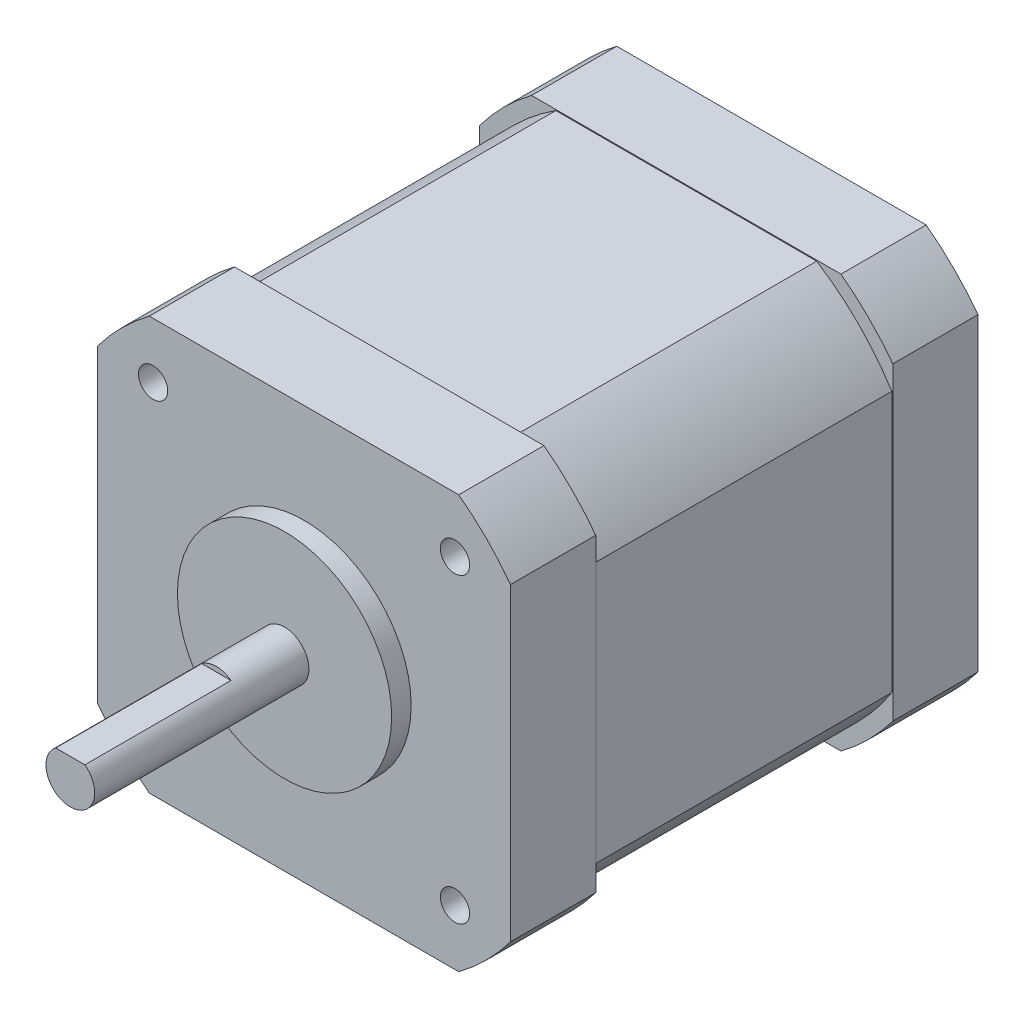
SolidWorks part; units mm, degrees
ref_plane "Front Plane" through (0, 0, 0) normal (0, 0, 1) x (1, 0, 0)
ref_plane "Top Plane" through (0, 0, 0) normal (0, 1, 0) x (1, 0, 0)
ref_plane "Right Plane" through (0, 0, 0) normal (1, 0, 0) x (0, 0, -1)
sketch "Sketch1" plane through (0, 0, 0) normal (0, 0, 1) x (1, 0, 0)
  line L0 (-21.209, 15.888) -> (-21.209, -15.888)
  line L1 (-15.888, -21.209) -> (15.888, -21.209)
  line L2 (21.209, -15.888) -> (21.209, 15.888)
  line L3 (15.888, 21.209) -> (-15.888, 21.209)
  arc A0 (-15.888, 21.209) -> (-21.209, 15.888) centre (0, 0) ccw
  arc A1 (-21.209, -15.888) -> (-15.888, -21.209) centre (0, 0) ccw
  arc A2 (15.888, -21.209) -> (21.209, -15.888) centre (0, 0) ccw
  arc A3 (21.209, 15.888) -> (15.888, 21.209) centre (0, 0) ccw
extrude "Boss-Extrude1" add sketch "Sketch1" against normal blind 8.75
sketch "Sketch2" plane through (0, 0, -8.75) normal (0, 0, -1) x (-1, 0, 0)
  line L0 (-13.3944, 21.109) -> (13.3944, 21.109)
  line L1 (21.109, 13.3944) -> (21.109, -13.3944)
  line L2 (13.3944, -21.109) -> (-13.3944, -21.109)
  line L3 (-21.109, -13.3944) -> (-21.109, 13.3944)
  arc A0 (-21.109, 13.3944) -> (-13.3944, 21.109) centre (0, 0) cw
  arc A1 (13.3944, 21.109) -> (21.109, 13.3944) centre (0, 0) cw
  arc A2 (21.109, -13.3944) -> (13.3944, -21.109) centre (0, 0) cw
  arc A3 (-13.3944, -21.109) -> (-21.109, -13.3944) centre (0, 0) cw
extrude "Boss-Extrude2" add sketch "Sketch2" along normal blind 30.5
ref_plane "Plane1" through (0, 0, -39.25) normal (0, 0, 1) x (1, 0, 0)
sketch "Sketch3" plane through (0, 0, -39.25) normal (0, 0, 1) x (1, 0, 0)
  line L0 (-15.888, -21.209) -> (15.888, -21.209)
  line L1 (21.209, -15.888) -> (21.209, 15.888)
  line L2 (15.888, 21.209) -> (-15.888, 21.209)
  line L3 (-21.209, 15.888) -> (-21.209, -15.888)
  arc A0 (-21.209, -15.888) -> (-15.888, -21.209) centre (0, 0) ccw
  arc A1 (15.888, -21.209) -> (21.209, -15.888) centre (0, 0) ccw
  arc A2 (21.209, 15.888) -> (15.888, 21.209) centre (0, 0) ccw
  arc A3 (-15.888, 21.209) -> (-21.209, 15.888) centre (0, 0) ccw
extrude "Boss-Extrude3" add sketch "Sketch3" against normal blind 8.75
sketch "Sketch4" plane through (0, 0, 0) normal (0, 0, 1) x (1, 0, 0)
  circle A0 centre (0, 0) radius 11
extrude "Boss-Extrude4" add sketch "Sketch4" along normal blind 2
sketch "Sketch5" plane through (0, 0, 2) normal (0, 0, 1) x (1, 0, 0)
  circle A0 centre (0, 0) radius 2.5
extrude "Boss-Extrude5" add sketch "Sketch5" along normal blind 22
sketch "Sketch6" plane through (0, 0, 24) normal (0, 0, 1) x (1, 0, 0)
  line L0 (-1.5, 2) -> (1.5, 2)
  arc A0 (1.5, 2) -> (-1.5, 2) centre (0, 0) ccw
extrude "Cut-Extrude1" cut sketch "Sketch6" against normal blind 15
hole_wizard "M3x0.5 Tapped Hole1" positions "Sketch8" profile "Sketch7" tap size "M3x0.5" standard "ANSI Metric"
sketch "Sketch8" plane through (0, 0, 0) normal (0, 0, 1) x (1, 0, 0)
  point P0 (-15.5, 15.5)
  point P1 (-15.5, -15.5)
  point P2 (15.5, -15.5)
  point P3 (15.5, 15.5)
sketch "Sketch7" plane through (-15.5, 15.5, 0) normal (1, 0, 0) x (0, -1, 0)
  line L0 (0, 0) -> (0, 8.2511)
  line L1 (0, 8.2511) -> (1.25, 7.5)
  line L2 (1.25, 7.5) -> (1.25, 6)
  line L3 (1.25, 6) -> (1.5, 6)
  line L4 (1.5, 6) -> (1.5, 0)
  line L5 (1.5, 0) -> (0, 0)
  line L10 (0, 8.2511) -> (-1.25, 7.5) construction
  line L11 (0, -6.35) -> (0, 107.95) construction
  dimension "Tap Drill Dia." = 2.5
  dimension "Tap Drill Depth" = 7.5
  dimension "Thread Major Dia." = 3
  dimension "Thread Depth" = 6
  dimension "Drill Angle" = 118
